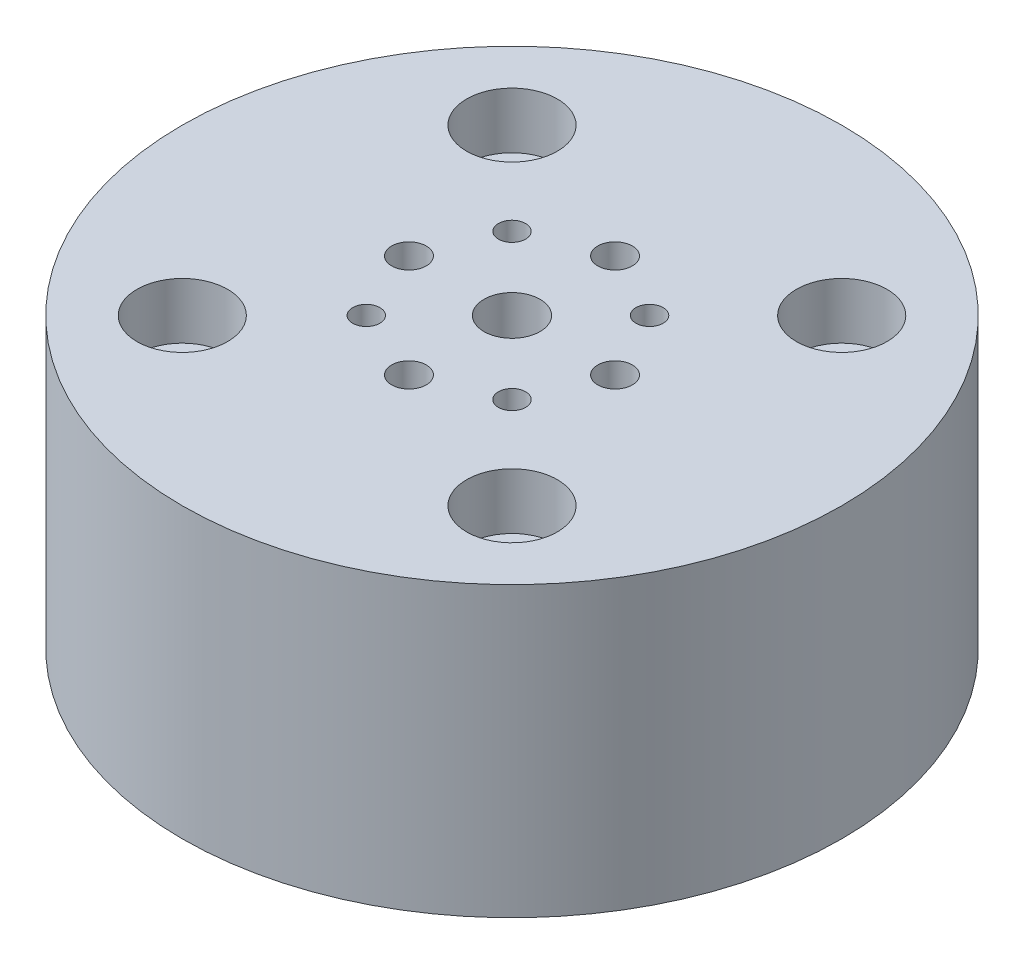
SolidWorks part; units mm, degrees
ref_plane "前视基准面" through (0, 0, 0) normal (0, 0, 1) x (1, 0, 0)
ref_plane "上视基准面" through (0, 0, 0) normal (0, 1, 0) x (1, 0, 0)
ref_plane "右视基准面" through (0, 0, 0) normal (1, 0, 0) x (0, 0, -1)
sketch "草图1" plane through (0, 0, 0) normal (0, 1, 0) x (1, 0, 0)
  circle A0 centre (0, 0) radius 40
  dimension "D1" = 80
extrude "凸台-拉伸1" add sketch "草图1" along normal blind 35
sketch "草图2" plane through (0, 35, 0) normal (0, 1, 0) x (1, 0, 0)
  line L0 (0, 0) -> (-15.3073, 36.9552)
  line L1 (-20, 20) -> (20, 20)
  line L2 (-20, 20) -> (-20, -20)
  line L3 (-20, -20) -> (20, -20)
  line L4 (20, 20) -> (20, -20)
  line L5 (-20, 20) -> (20, -20) construction
  line L6 (-20, -20) -> (20, 20) construction
  circle A0 centre (0, 0) radius 12.5
  circle A1 centre (0, 0) radius 40 construction
  point P0 (0, 0)
  point P8 (8.8388, 8.8388)
  point P9 (0, 12.5)
  point P10 (-8.8388, 8.8388)
  point P11 (-12.5, 0)
  point P12 (-8.8388, -8.8388)
  point P13 (0, -12.5)
  point P14 (8.8388, -8.8388)
  point P15 (12.5, 0)
  dimension "D3" = 25
  dimension "D1" = 40
  dimension "D2" = 40
  dimension "D4" = 0
  dimension "D5" = 22.5
hole_wizard "打孔尺寸(%根据)内六角圆柱头螺钉的类型1" positions "3D草图1" profile "草图3" counterbore size "M6" standard "GB"
sketch3d "3D草图1"
  point P0 (-20, 35, -20)
  point P3 (20, 35, -20)
  point P6 (20, 35, 20)
  point P9 (-20, 35, 20)
sketch "草图3" plane through (-20, 35, -20) normal (1, 0, 0) x (0, 0, 1)
  line L0 (0, 0) -> (0, 51.9828)
  line L1 (0, 51.9828) -> (3.3, 50)
  line L2 (3.3, 50) -> (3.3, 6.8)
  line L3 (3.3, 6.8) -> (5.5, 6.8)
  line L4 (5.5, 6.8) -> (5.5, 0)
  line L5 (5.5, 0) -> (0, 0)
  line L10 (0, 51.9828) -> (-3.3, 50) construction
  line L11 (0, -6.35) -> (0, 107.95) construction
  dimension "孔直径" = 6.6
  dimension "孔深度" = 50
  dimension "柱形沉头孔直径" = 11
  dimension "柱形沉头孔深度" = 6.8
  dimension "导头角度" = 118
hole_wizard "M5 螺纹孔1" positions "3D草图2" profile "草图4" tap size "M5" standard "GB"
sketch3d "3D草图2"
  point P0 (0, 35, -12.5)
  point P3 (0, 35, 12.5)
  point P6 (12.5, 35, 0)
  point P9 (-12.5, 35, 0)
sketch "草图4" plane through (0, 35, -12.5) normal (1, 0, 0) x (0, 0, 1)
  line L0 (0, 0) -> (0, 13.6618)
  line L1 (0, 13.6618) -> (2.1, 12.4)
  line L2 (2.1, 12.4) -> (2.1, 0)
  line L5 (2.1, 0) -> (0, 0)
  line L10 (0, 13.6618) -> (-2.1, 12.4) construction
  line L11 (0, -6.35) -> (0, 107.95) construction
  dimension "螺纹孔钻头直径" = 4.2
  dimension "螺纹孔钻头深度" = 12.4
  dimension "导头角度" = 118
cosmetic thread "孔螺蚊线1"
cosmetic thread "孔螺蚊线2"
cosmetic thread "孔螺蚊线3"
cosmetic thread "孔螺蚊线4"
hole_wizard "M4 螺纹孔1" positions "3D草图3" profile "草图5" tap size "M4" standard "GB"
sketch3d "3D草图3"
  line L0 (-20, 35, 20) -> (20, 35, -20) construction
  point P0 (-8.8388, 35, -8.8388)
  point P3 (8.3437, 35, -8.3437)
  point P7 (8.8388, 35, 8.8388)
  point P10 (-8.8388, 35, 8.8388)
sketch "草图5" plane through (-8.8388, 35, -8.8388) normal (1, 0, 0) x (0, 0, 1)
  line L0 (0, 0) -> (0, 11.0914)
  line L1 (0, 11.0914) -> (1.65, 10.1)
  line L2 (1.65, 10.1) -> (1.65, 0)
  line L5 (1.65, 0) -> (0, 0)
  line L10 (0, 11.0914) -> (-1.65, 10.1) construction
  line L11 (0, -6.35) -> (0, 107.95) construction
  dimension "螺纹孔钻头直径" = 3.3
  dimension "螺纹孔钻头深度" = 10.1
  dimension "导头角度" = 118
cosmetic thread "孔螺蚊线5"
cosmetic thread "孔螺蚊线6"
cosmetic thread "孔螺蚊线7"
cosmetic thread "孔螺蚊线8"
hole_wizard "M8 螺纹孔1" positions "3D草图4" profile "草图6" tap size "M8" standard "GB"
sketch3d "3D草图4"
  point P0 (0, 35, 0)
sketch "草图6" plane through (0, 35, 0) normal (1, 0, 0) x (0, 0, 1)
  line L0 (0, 0) -> (0, 21.7929)
  line L1 (0, 21.7929) -> (3.4, 19.75)
  line L2 (3.4, 19.75) -> (3.4, 0)
  line L5 (3.4, 0) -> (0, 0)
  line L10 (0, 21.7929) -> (-3.4, 19.75) construction
  line L11 (0, -6.35) -> (0, 107.95) construction
  dimension "螺纹孔钻头直径" = 6.8
  dimension "螺纹孔钻头深度" = 19.75
  dimension "导头角度" = 118
cosmetic thread "孔螺蚊线9" parameters "D1"=16, "D2"=8
ref_plane "基准面2" through (-15.3073, 35, -36.9552) normal (-0.3827, 0, -0.9239) x (-0.9239, 0, 0.3827)
sketch "草图7" plane through (-15.3073, 35, -36.9552) normal (-0.3827, 0, -0.9239) x (-0.9239, 0, 0.3827)
  line L0 (0, 0) -> (0, -35) construction
  line L1 (40, 0) -> (-40, 0) construction
  circle A0 centre (0, -10) radius 2.065
  point P4 (0, -10)
  dimension "D2" = 4.13
  dimension "D1" = 10
extrude "切除-拉伸1" cut sketch "草图7" against normal blind 40 contours A0
